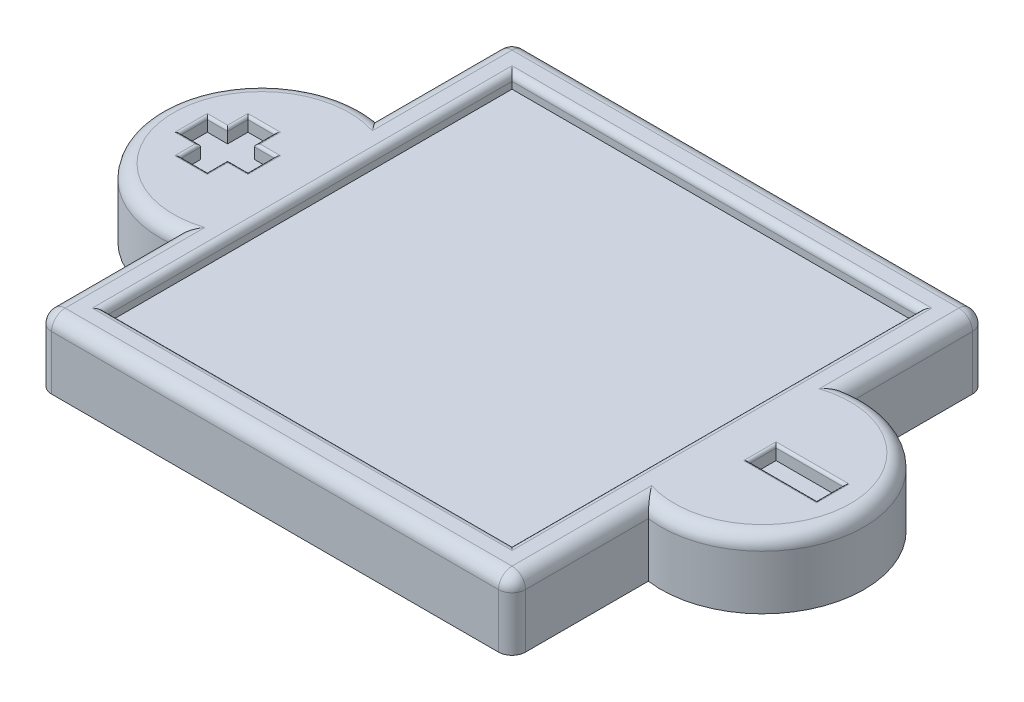
SolidWorks part; units mm, degrees
ref_plane "Front" through (0, 0, 0) normal (0, 0, 1) x (1, 0, 0)
ref_plane "Top" through (0, 0, 0) normal (0, 1, 0) x (1, 0, 0)
ref_plane "Right" through (0, 0, 0) normal (1, 0, 0) x (0, 0, -1)
sketch "Sketch1" plane through (0, 0, 0) normal (0, 1, 0) x (1, 0, 0)
  line L0 (-52.1845, -7.2686) -> (-54.7245, -7.2686) construction
  line L1 (-52.1845, 37.1814) -> (36.7155, 37.1814)
  line L2 (-52.1845, 37.1814) -> (-52.1845, -51.7186)
  line L3 (-52.1845, -51.7186) -> (36.7155, -51.7186)
  line L4 (36.7155, 37.1814) -> (36.7155, -51.7186)
  line L5 (36.7155, -7.2686) -> (39.2555, -7.2686) construction
  circle A0 centre (-54.7245, -7.2686) radius 19.05
  circle A1 centre (39.2555, -7.2686) radius 19.05
  dimension "D5" = 38.1
  dimension "D6" = 38.1
  dimension "D1" = 88.9
  dimension "D2" = 88.9
  dimension "D3" = 2.54
  dimension "D4" = 2.54
extrude "Boss-Extrude1" add sketch "Sketch1" along normal blind 12.7 contours L2 A0 | L2 A0 | A1 L4 L1 L2 A0 L3 | L4 A1 | L4 A1
sketch "Sketch2" plane through (0, 12.7, 0) normal (0, 1, 0) x (1, 0, 0)
  line L0 (-52.1845, 37.1814) -> (-52.1845, 11.6114) construction
  line L1 (-45.8345, 30.8314) -> (30.3655, 30.8314)
  line L2 (-45.8345, 30.8314) -> (-45.8345, -45.3686)
  line L3 (-45.8345, -45.3686) -> (30.3655, -45.3686)
  line L4 (30.3655, 30.8314) -> (30.3655, -45.3686)
  line L5 (-52.1845, -51.7186) -> (36.7155, -51.7186) construction
  dimension "D1" = 76.2
  dimension "D2" = 76.2
  dimension "D3" = 6.35
  dimension "D4" = 6.35
extrude "Cut-Extrude1" cut sketch "Sketch2" against normal blind 2.54
sketch "Sketch3" plane through (0, 12.7, 0) normal (0, 1, 0) x (1, 0, 0)
  line L0 (-73.7745, -7.2686) -> (-61.0745, -7.2686) construction
  line L1 (58.3055, -7.2686) -> (45.6055, -7.2686) construction
  line L2 (-52.1845, 37.1814) -> (36.7155, 37.1814) construction
  line L3 (39.2555, -4.7286) -> (51.9555, -4.7286)
  line L4 (39.2555, -4.7286) -> (39.2555, -9.8086)
  line L5 (39.2555, -9.8086) -> (51.9555, -9.8086)
  line L6 (51.9555, -4.7286) -> (51.9555, -9.8086)
  line L7 (36.7155, 37.1814) -> (-7.7345, 37.1814) construction
  line L8 (-7.7345, 37.1814) -> (-7.7345, -51.7186) construction
  line L9 (-52.1845, -51.7186) -> (36.7155, -51.7186) construction
  line L10 (-67.4245, -4.7286) -> (-67.4245, -9.8086)
  line L11 (-54.7245, -9.8086) -> (-67.4245, -9.8086)
  line L12 (-54.7245, -4.7286) -> (-54.7245, -9.8086)
  line L13 (-54.7245, -4.7286) -> (-67.4245, -4.7286)
  line L14 (-61.0745, -7.2686) -> (-36.5177, -31.8254) construction
  line L15 (-63.6145, -13.6186) -> (-58.5345, -13.6186)
  line L16 (-58.5345, -13.6186) -> (-58.5345, -0.9186)
  line L17 (-63.6145, -0.9186) -> (-58.5345, -0.9186)
  line L18 (-63.6145, -13.6186) -> (-63.6145, -0.9186)
  arc A0 (-52.1845, 11.6114) -> (-52.1845, -26.1485) centre (-54.7245, -7.2686) ccw construction
  arc A1 (36.7155, -26.1485) -> (36.7155, 11.6114) centre (39.2555, -7.2686) ccw construction
  dimension "D1" = 12.7
  dimension "D2" = 12.7
  dimension "D3" = 5.08
  dimension "D4" = 12.7
  dimension "D5" = 2.54
  dimension "D6" = 6.35
extrude "Cut-Extrude2" cut sketch "Sketch3" against normal blind 2.54 contours L18 L13 L16 L17 | L11 L18 L13 L10 | L18 L11 L16 L13 | L16 L11 L12 L13 | L18 L15 L16 L11 | L6 L3 L4 L5
sketch "Sketch4" plane through (0, 0, 0) normal (0, -1, 0) x (1, 0, 0)
  line L0 (-52.1845, 51.7186) -> (36.7155, -37.1814) construction
  line L1 (36.7155, -37.1814) -> (-7.7345, 7.2686) construction
  line L2 (-7.7345, 7.2686) -> (36.7155, 7.2686) construction
  line L3 (36.7155, 7.2686) -> (14.4905, 7.2686) construction
  line L4 (-7.7345, 7.2686) -> (-52.1845, 7.2686) construction
  line L5 (-52.1845, 7.2686) -> (-29.9595, 7.2686) construction
  circle A0 centre (-29.9595, 7.2686) radius 3.5
  circle A1 centre (14.4905, 7.2686) radius 3.5
  dimension "D1" = 7
  dimension "D2" = 7
extrude "Cut-Extrude4" cut sketch "Sketch4" against normal blind 5
fillet "Fillet8" radius 0.508 2 edges at (14.4905, 0, 3.7686) (-29.9595, 0, 3.7686)
fillet "Fillet9" radius 2.54 12 edges at (36.7155, 6.35, 51.7186) (-52.1845, 6.35, 51.7186) (-52.1845, 6.35, -37.1814) (36.7155, 6.35, -37.1814) (36.7155, 12.7, 38.9335) (-7.7345, 12.7, 51.7186) (-52.1845, 12.7, 38.9335) (-73.7745, 12.7, 7.2686) (-52.1845, 12.7, -24.3964) (-7.7345, 12.7, -37.1814) (36.7155, 12.7, -24.3964) (58.3055, 12.7, 7.2686)
fillet "Fillet10" radius 0.508 16 edges at (-56.6295, 12.7, 4.7286) (-58.5345, 12.7, 2.8236) (-61.0745, 12.7, 0.9186) (-63.6145, 12.7, 2.8236) (-65.5195, 12.7, 4.7286) (-67.4245, 12.7, 7.2686) (-65.5195, 12.7, 9.8086) (-63.6145, 12.7, 11.7136) (-61.0745, 12.7, 13.6186) (-58.5345, 12.7, 11.7136) (-56.6295, 12.7, 9.8086) (-54.7245, 12.7, 7.2686) (39.2555, 12.7, 7.2686) (45.6055, 12.7, 4.7286) (45.6055, 12.7, 9.8086) (51.9555, 12.7, 7.2686)
fillet "Fillet11" radius 1.27 4 edges at (-45.8345, 12.7, 7.2686) (-7.7345, 12.7, 45.3686) (-7.7345, 12.7, -30.8314) (30.3655, 12.7, 7.2686)
